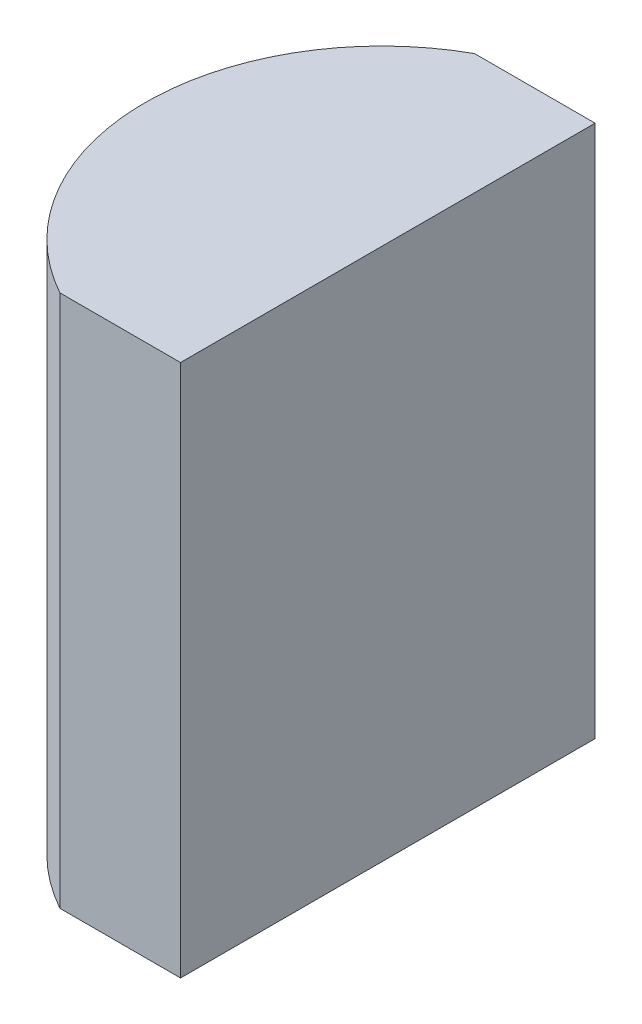
SolidWorks part; units mm, degrees
ref_plane "前视基准面" through (0, 0, 0) normal (0, 0, 1) x (1, 0, 0)
ref_plane "上视基准面" through (0, 0, 0) normal (0, 1, 0) x (1, 0, 0)
ref_plane "右视基准面" through (0, 0, 0) normal (1, 0, 0) x (0, 0, -1)
sketch "草图1" plane through (0, 0, 0) normal (0, 1, 0) x (1, 0, 0)
  line L0 (0, 0) -> (10.0716, 0) construction
  line L1 (2.4187, 3.5) -> (4.4552, 3.5)
  line L2 (2.4187, -3.5) -> (4.4552, -3.5)
  line L3 (4.4552, 3.5) -> (4.4552, -3.5)
  arc A0 (2.4187, 3.5) -> (2.4187, -3.5) centre (4.3552, 0) ccw
  point P2 (0.3552, 0)
  point P4 (4.4552, 0)
  dimension "D2" = 3.5
  dimension "D3" = 4
  dimension "D4" = 4.1
  dimension "D1" = 3.5
extrude "凸台-拉伸1" add sketch "草图1" along normal blind 9
